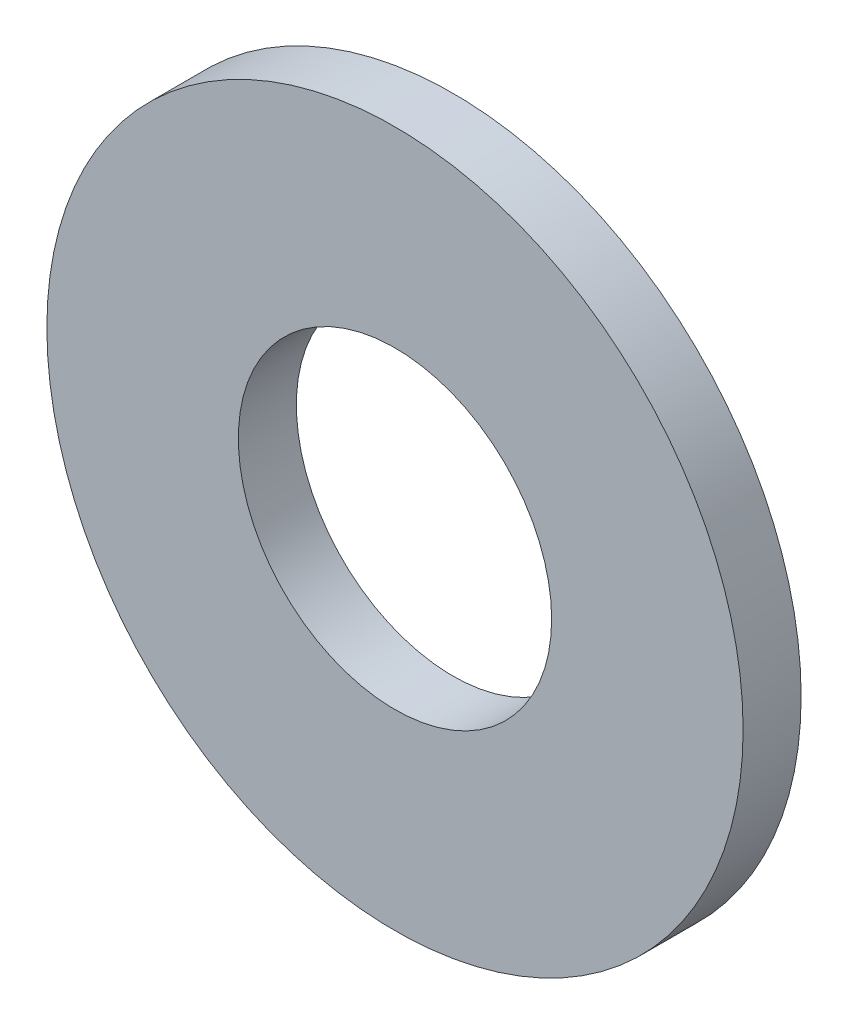
SolidWorks part; units mm, degrees
ref_plane "Front Plane" through (0, 0, 0) normal (0, 0, 1) x (1, 0, 0)
ref_plane "Top Plane" through (0, 0, 0) normal (0, 1, 0) x (1, 0, 0)
ref_plane "Right Plane" through (0, 0, 0) normal (1, 0, 0) x (0, 0, -1)
sketch "Sketch1" plane through (0, 0, 0) normal (0, 0, 1) x (1, 0, 0)
  circle A0 centre (0, 0) radius 1.35
  circle A1 centre (0, 0) radius 3
  dimension "D1" = 2.7
  dimension "D2" = 6
extrude "Boss-Extrude1" add sketch "Sketch1" along normal blind 0.5
